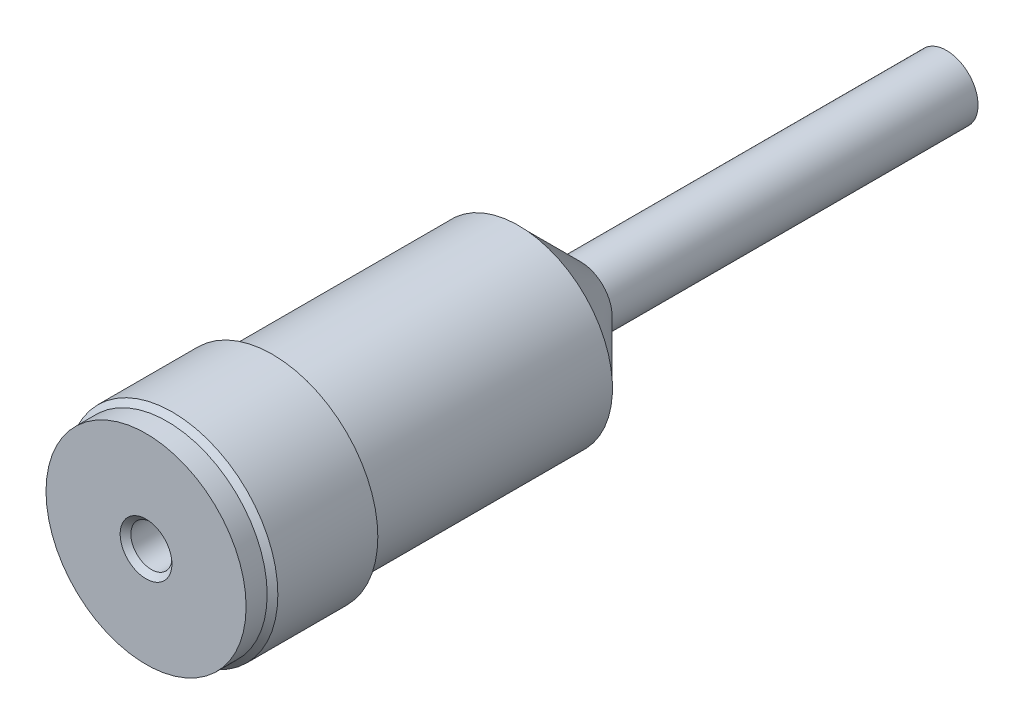
SolidWorks part; units mm, degrees
material "PEEK"
ref_plane "Front" through (0, 0, 0) normal (0, 0, 1) x (1, 0, 0)
ref_plane "Top" through (0, 0, 0) normal (0, 1, 0) x (1, 0, 0)
ref_plane "Right" through (0, 0, 0) normal (1, 0, 0) x (0, 0, -1)
sketch "Sketch1" plane through (0, 0, 0) normal (0, 0, 1) x (1, 0, 0)
  circle A0 centre (0, 0) radius 5.0038
  dimension "D1" = 10.0076
extrude "Extrude1" add sketch "Sketch1" against normal blind 37
sketch "Sketch2" plane through (0, 0, 0) normal (0, 0, 1) x (1, 0, 0)
  circle A0 centre (0, 0) radius 0.9746
  dimension "D1" = 1.9492
extrude "Extrude2" cut sketch "Sketch2" against normal blind 7.5
fillet "Fillet1" [suppressed] radius 0.508
sketch "Sketch3" plane through (0, 0, -37) normal (0, 0, -1) x (-1, 0, 0)
  circle A0 centre (0, 0) radius 1.5
  dimension "D1" = 3
extrude "Extrude3" cut sketch "Sketch3" against normal blind 20.32 flip side to cut
fillet "Fillet2" [suppressed] radius 0.508
sketch "Sketch5" plane through (0, 0, 0) normal (1, 0, 0) x (0, 0, -1)
  circle A0 centre (7, 0) radius 0.635
  dimension "D1" = 1.27
  dimension "D2" = 7
extrude "Extrude4" cut sketch "Sketch5" against normal blind 20.32
chamfer "Chamfer2" distance 0.254 angle 45 1 edges at (5.0038, 0, 0)
sketch "Sketch6" plane through (0, 0, 0) normal (0, 1, 0) x (1, 0, 0)
  line L2 (-4.7498, 0) -> (4.7498, 0) construction
  line L3 (-5.0038, 16.68) -> (-4.4638, 16.68)
  line L4 (-5.0038, 16.68) -> (-5.0038, 5)
  line L6 (-5.0038, 5) -> (-4.4638, 5)
  line L9 (-4.4638, 16.68) -> (-4.4638, 5)
  dimension "D1" = 0.54
  dimension "D2" = 5
revolve "Cut-Revolve1" cut sketch "Sketch6" angle 360 about axis through (0, 0, -37) along (0, 0, 1)
chamfer "Chamfer3" distance 2.9464 angle 45 1 edges at (-1.5, 0, -16.68)
sketch "Sketch8" plane through (0, 0, 0) normal (0, 0, 1) x (1, 0, 0)
  circle A1 centre (0, 0) radius 4.7498
  circle A2 centre (0, 0) radius 0.9746
extrude "Boss-Extrude1" add sketch "Sketch8" along normal blind 1
chamfer "Chamfer4" distance 0.254 angle 45 1 edges at (0.9746, 0, 1)
